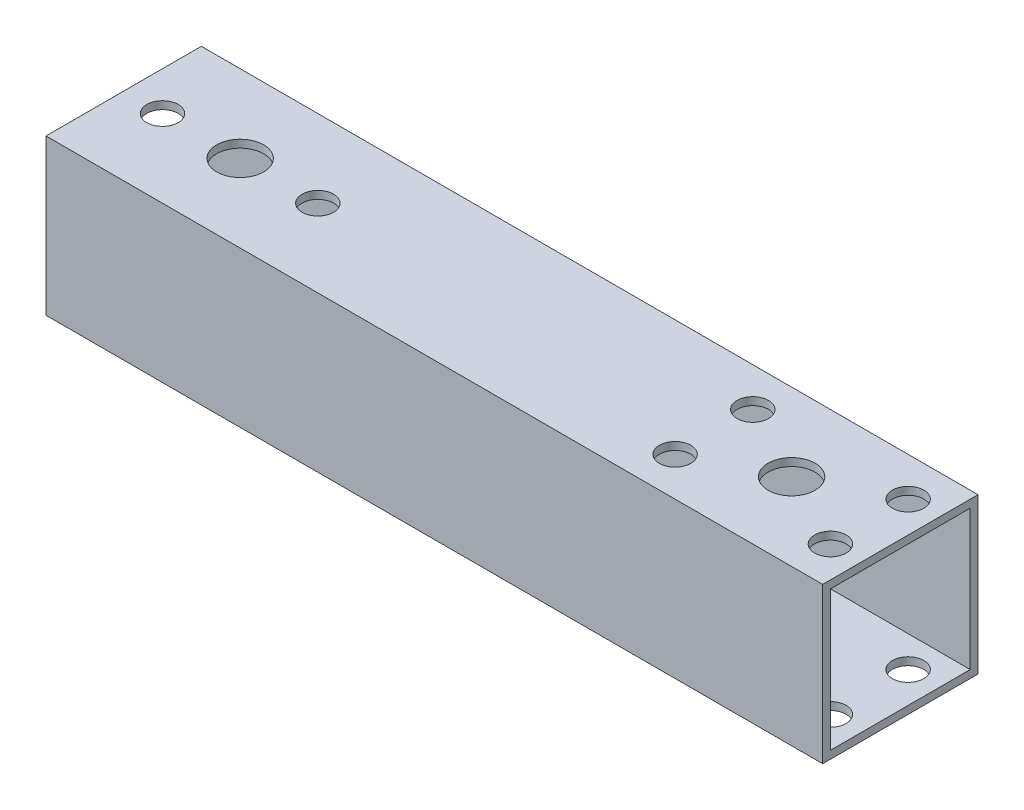
SolidWorks part; units mm, degrees
material "1060 合金"
ref_plane "前视基准面" through (0, 0, 0) normal (0, 0, 1) x (1, 0, 0)
ref_plane "上视基准面" through (0, 0, 0) normal (0, 1, 0) x (1, 0, 0)
ref_plane "右视基准面" through (0, 0, 0) normal (1, 0, 0) x (0, 0, -1)
other "Configuration Table"
sketch "草图1" plane through (0, 0, 0) normal (1, 0, 0) x (0, 0, -1)
  line L0 (-10, -10) -> (-10, 10)
  line L1 (-9, -9) -> (9, -9)
  line L2 (-9, -9) -> (-9, 9)
  line L3 (-9, 9) -> (9, 9)
  line L4 (9, -9) -> (9, 9)
  line L5 (-9, -9) -> (9, 9) construction
  line L6 (-9, 9) -> (9, -9) construction
  line L7 (-10, 10) -> (10, 10)
  line L8 (10, -10) -> (10, 10)
  line L9 (-10, -10) -> (10, -10)
  point P0 (0, 0)
  dimension "D2" = 20
  dimension "D1" = 1
extrude "凸台-拉伸1" add sketch "草图1" along normal mid plane 100
sketch "草图2" plane through (0, 10, 0) normal (0, 1, 0) x (1, 0, 0)
  line L0 (36, 0) -> (0, 0) construction
  line L1 (26, -5) -> (46, -5) construction
  line L2 (26, -5) -> (26, 5) construction
  line L3 (26, 5) -> (46, 5) construction
  line L4 (46, -5) -> (46, 5) construction
  line L5 (26, -5) -> (46, 5) construction
  line L6 (26, 5) -> (46, -5) construction
  line L9 (-45, 0) -> (-25, 0) construction
  line L11 (0, 0) -> (-45, 0) construction
  line L13 (50, 10) -> (50, -10) construction
  line L14 (-50, 10) -> (-50, -10) construction
  circle A0 centre (26, 5) radius 2.025
  circle A1 centre (46, 5) radius 2.025
  circle A2 centre (46, -5) radius 2.025
  circle A3 centre (26, -5) radius 2.025
  circle A4 centre (36, 0) radius 3.025
  circle A5 centre (-45, 0) radius 2.025
  circle A6 centre (-25, 0) radius 2.025
  circle A7 centre (-35, 0) radius 3.025
  point P0 (36, 0)
  point P18 (-35, 0)
  dimension "D4" = 6.05
  dimension "D5" = 4.05
  dimension "D6" = 5
  dimension "D1" = 10
  dimension "D2" = 4
  dimension "D3" = 20
  dimension "D7" = 20
extrude "切除-拉伸1" cut sketch "草图2" against normal blind 40
